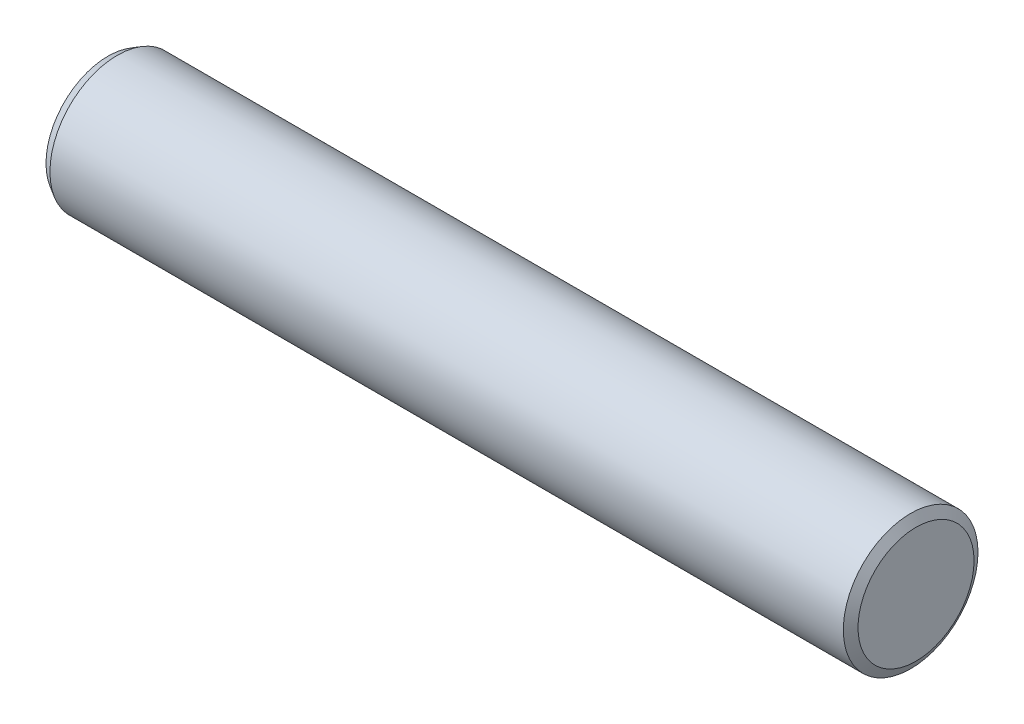
SolidWorks part; units mm, degrees
ref_plane "Front Plane" through (0, 0, 0) normal (0, 0, 1) x (1, 0, 0)
ref_plane "Top Plane" through (0, 0, 0) normal (0, 1, 0) x (1, 0, 0)
ref_plane "Right Plane" through (0, 0, 0) normal (1, 0, 0) x (0, 0, -1)
sketch "Sketch1" plane through (0, 0, 0) normal (0, 0, 1) x (1, 0, 0)
  line L1 (0, 0) -> (-30, 0)
  line L2 (0, 0) -> (0, 2.5)
  line L3 (0, 2.5) -> (-30, 2.5)
  line L4 (-30, 0) -> (-30, 2.5)
  line L5 (0, 0) -> (-30, 2.5) construction
  line L6 (0, 2.5) -> (-30, 0) construction
  point P4 (-15, 1.25)
  dimension "D1" = 30
  dimension "D2" = 2.5
revolve "Revolve1" add sketch "Sketch1" angle 360 about L1
chamfer "Chamfer1" distance 0.2 angle 60 2 edges at (-30, 0, -2.5) (0, 0, -2.5)
ref_plane "Plane1" through (-15, 0, 0) normal (1, 0, 0) x (0, 0, -1)
